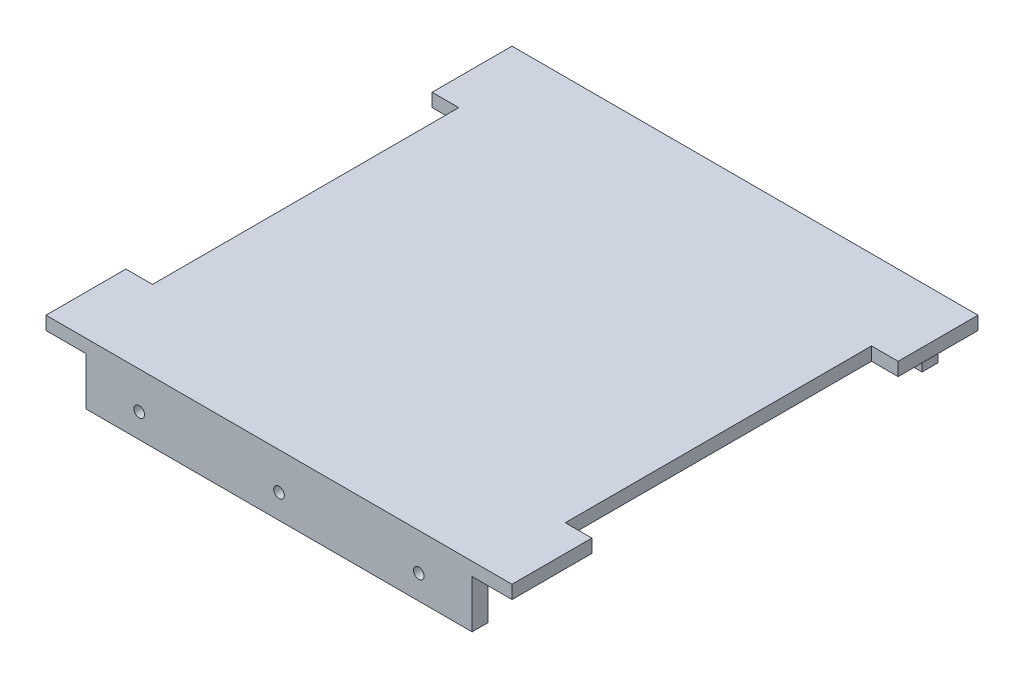
SolidWorks part; units mm, degrees
ref_plane "Front Plane" through (0, 0, 0) normal (0, 0, 1) x (1, 0, 0)
ref_plane "Top Plane" through (0, 0, 0) normal (0, 1, 0) x (1, 0, 0)
ref_plane "Right Plane" through (0, 0, 0) normal (1, 0, 0) x (0, 0, -1)
sketch "Sketch1" plane through (0, 0, 0) normal (0, 1, 0) x (1, 0, 0)
  line L1 (-111.5458, 60.1145) -> (63.4542, 60.1145)
  line L2 (-111.5458, 60.1145) -> (-111.5458, -114.8855)
  line L3 (-111.5458, -114.8855) -> (63.4542, -114.8855)
  line L4 (63.4542, 60.1145) -> (63.4542, -114.8855)
  dimension "D1" = 175
  dimension "D2" = 175
extrude "Boss-Extrude1" add sketch "Sketch1" along normal blind 5
sketch "Sketch3" plane through (0, 0, 0) normal (0, -1, 0) x (1, 0, 0)
  line L0 (63.4542, -60.1145) -> (-111.5458, -60.1145) construction
  line L1 (-96.5458, 114.8855) -> (48.4542, 114.8855)
  line L2 (-96.5458, 114.8855) -> (-96.5458, 108.8855)
  line L3 (-96.5458, 108.8855) -> (48.4542, 108.8855)
  line L4 (48.4542, 114.8855) -> (48.4542, 108.8855)
  line L5 (-96.5458, -60.1145) -> (48.4542, -60.1145)
  line L6 (-96.5458, -60.1145) -> (-96.5458, -54.1145)
  line L7 (-96.5458, -54.1145) -> (48.4542, -54.1145)
  line L8 (48.4542, -60.1145) -> (48.4542, -54.1145)
  line L9 (-111.5458, -60.1145) -> (-111.5458, 114.8855) construction
  line L10 (63.4542, 114.8855) -> (63.4542, -60.1145) construction
  point P15 (0, 0)
  dimension "D1" = 6
  dimension "D2" = 145
  dimension "D3" = 6
  dimension "D4" = 15
  dimension "D5" = 15
  dimension "D6" = 160
extrude "Boss-Extrude3" add sketch "Sketch3" along normal blind 18
sketch "Sketch4" plane through (0, 0, -60.1145) normal (0, 0, -1) x (-1, 0, 0)
  line L0 (-48.4542, -18) -> (-48.4542, 0) construction
  line L1 (96.5458, -18) -> (96.5458, 0) construction
  circle A0 centre (-28.4542, -8.9008) radius 2
  circle A1 centre (24.0458, -8.9008) radius 2
  circle A2 centre (76.5458, -8.9008) radius 2
  dimension "D1" = 20
  dimension "D2" = 20
  dimension "D3" = 52.5
extrude "Cut-Extrude2" cut sketch "Sketch4" against normal through all both and the other way through all
sketch "Sketch5" plane through (0, 5, 0) normal (0, 1, 0) x (1, 0, 0)
  line L0 (-111.5458, 60.1145) -> (-111.5458, -114.8855) construction
  line L1 (-111.5458, 30.1145) -> (-101.5458, 30.1145)
  line L2 (-111.5458, 30.1145) -> (-111.5458, -84.8855)
  line L3 (-111.5458, -84.8855) -> (-101.5458, -84.8855)
  line L4 (-101.5458, 30.1145) -> (-101.5458, -84.8855)
  line L5 (63.4542, 60.1145) -> (-111.5458, 60.1145) construction
  line L6 (-111.5458, -114.8855) -> (63.4542, -114.8855) construction
  line L7 (63.4542, -114.8855) -> (63.4542, 60.1145) construction
  line L8 (63.4542, 30.1145) -> (53.4542, 30.1145)
  line L9 (63.4542, 30.1145) -> (63.4542, -84.8855)
  line L10 (63.4542, -84.8855) -> (53.4542, -84.8855)
  line L11 (53.4542, 30.1145) -> (53.4542, -84.8855)
  dimension "D1" = 30
  dimension "D2" = 30
  dimension "D3" = 10
  dimension "D4" = 10
extrude "Cut-Extrude3" cut sketch "Sketch5" against normal blind 10
